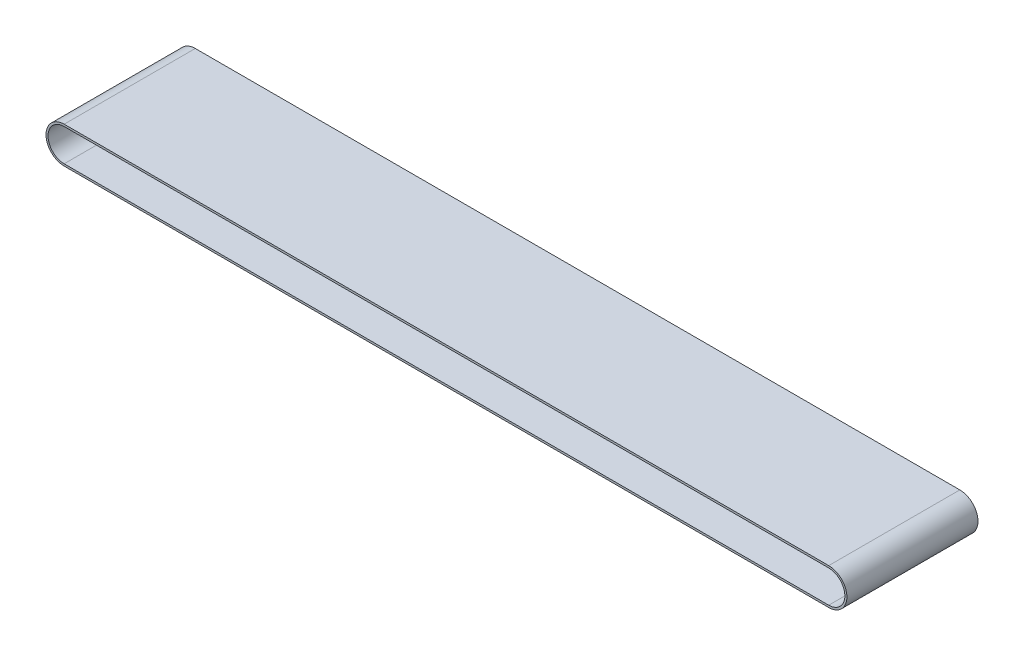
SolidWorks part; units mm, degrees
ref_plane "Alzado" through (0, 0, 0) normal (0, 0, 1) x (1, 0, 0)
ref_plane "Planta" through (0, 0, 0) normal (0, 1, 0) x (1, 0, 0)
ref_plane "Vista lateral" through (0, 0, 0) normal (1, 0, 0) x (0, 0, -1)
sketch "Croquis1" plane through (0, 0, 0) normal (0, 0, 1) x (1, 0, 0)
  line L0 (0, 0) -> (758, 0)
  line L1 (0, -32) -> (758, -32)
  line L2 (0, 2) -> (758, 2)
  line L3 (0, -34) -> (758, -34)
  arc A0 (0, 0) -> (0, -32) centre (0, -16) ccw
  arc A1 (758, 0) -> (758, -32) centre (758, -16) cw
  arc A2 (0, 2) -> (0, -34) centre (0, -16) ccw
  arc A3 (758, 2) -> (758, -34) centre (758, -16) cw
  point P11 (774, -16)
  point P13 (-33.5256, -178.9112)
  point P14 (0, -21.6642)
  point P15 (776, -16)
  dimension "D1" = 32
  dimension "D2" = 758
  dimension "D3" = 36
  dimension "D4" = 2
extrude "Saliente-Extruir1" add sketch "Croquis1" along normal blind 130
